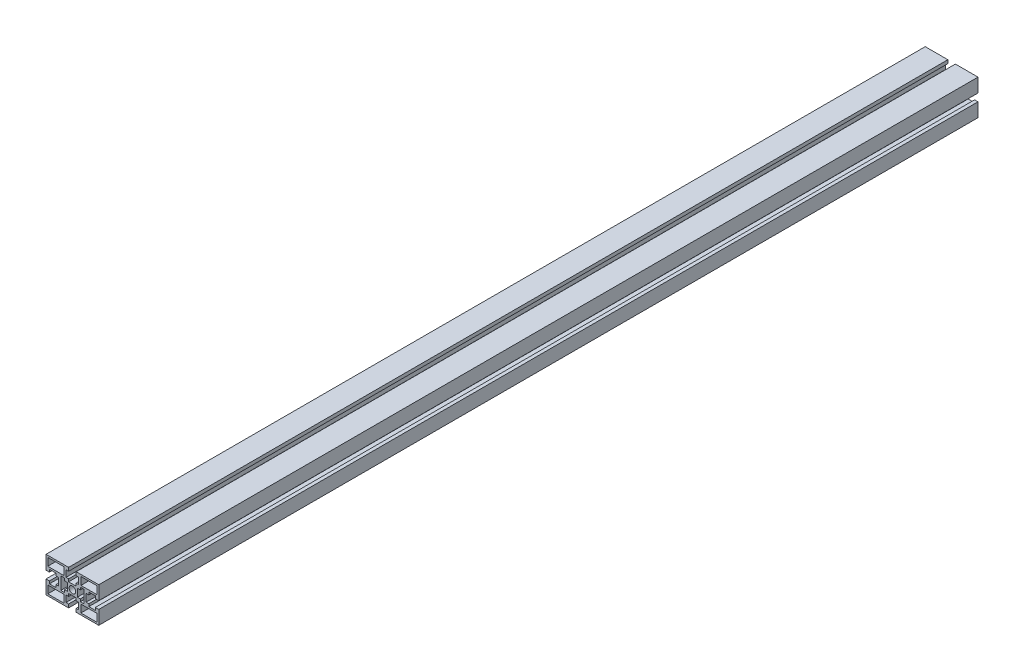
SolidWorks part; units mm, degrees
material "6063 T5"
ref_plane "Спереди" through (0, 0, 0) normal (0, 0, 1) x (1, 0, 0)
ref_plane "Сверху" through (0, 0, 0) normal (0, 1, 0) x (1, 0, 0)
ref_plane "Справа" through (0, 0, 0) normal (1, 0, 0) x (0, 0, -1)
sketch "Эскиз1" plane through (0, 0, 0) normal (0, 0, 1) x (1, 0, 0)
  line L0 (-29.9268, 29.4161) -> (30.0732, 29.4161) construction
  line L1 (0, 20) -> (0, -20) construction
  line L2 (-30, 0) -> (30, 0) construction
  line L3 (-30, 7.2) -> (-30, 20)
  line L4 (-30, 20) -> (-7.2, 20)
  line L5 (-13.2, -7.2) -> (-13.2, 7.2)
  line L6 (-28, 18) -> (-9.7, 18)
  line L7 (-28, 18) -> (-28, 9.2)
  line L8 (-28, 9.2) -> (-9.7, 9.2)
  line L9 (-9.7, 18) -> (-9.7, 9.2)
  line L10 (-13.2, 7.2) -> (-9, 7.2)
  line L11 (-9, 7.2) -> (-9, 4.4)
  line L12 (-9, 4.4) -> (-5.7, 4.4)
  line L13 (-5.7, 4.4) -> (-5.7, -4.4)
  line L14 (-9, -4.4) -> (-5.7, -4.4)
  line L15 (-9, -7.2) -> (-9, -4.4)
  line L16 (-13.2, -7.2) -> (-9, -7.2)
  line L17 (-28, -9.2) -> (-9.7, -9.2)
  line L18 (-9.7, -18) -> (-9.7, -9.2)
  line L19 (-28, -18) -> (-9.7, -18)
  line L20 (-28, -18) -> (-28, -9.2)
  line L21 (-30, -7.2) -> (-30, -20)
  line L22 (-30, -20) -> (-7.2, -20)
  line L23 (28, -18) -> (28, -9.2)
  line L24 (28, -18) -> (9.7, -18)
  line L25 (9.7, -18) -> (9.7, -9.2)
  line L26 (28, -9.2) -> (9.7, -9.2)
  line L27 (9, 4.4) -> (5.7, 4.4)
  line L28 (9, 7.2) -> (9, 4.4)
  line L29 (13.2, 7.2) -> (9, 7.2)
  line L30 (13.2, -7.2) -> (13.2, 7.2)
  line L31 (13.2, -7.2) -> (9, -7.2)
  line L32 (9, -7.2) -> (9, -4.4)
  line L33 (9, -4.4) -> (5.7, -4.4)
  line L34 (5.7, 4.4) -> (5.7, -4.4)
  line L35 (28, 9.2) -> (9.7, 9.2)
  line L36 (9.7, 18) -> (9.7, 9.2)
  line L37 (28, 18) -> (9.7, 18)
  line L38 (28, 18) -> (28, 9.2)
  line L39 (7.2, 20) -> (30, 20)
  line L40 (30, 20) -> (30, 7.2)
  line L41 (30, -7.2) -> (30, -20)
  line L42 (30, -20) -> (7.2, -20)
  circle A0 centre (0, 0) radius 3.75
  point P8 (0, 20)
  point P10 (-30, 0)
  point P25 (-5.7, 0)
  point P28 (-13.2, 0)
  line B0 (-7.2, 20) -> (-4.3, 20)
  line B1 (-4.3, 20) -> (-4.3, 16.1)
  line B2 (-4.3, 16.1) -> (-7.2, 16.1)
  line B3 (-7.2, 16.1) -> (-7.2, 8.7)
  line B4 (-7.2, 8.7) -> (-4.3, 8.7)
  line B5 (-4.3, 8.7) -> (-4.3, 5.7)
  line B6 (-4.3, 5.7) -> (4.3, 5.7)
  line B7 (4.3, 5.7) -> (4.3, 8.7)
  line B8 (4.3, 8.7) -> (7.2, 8.7)
  line B9 (7.2, 8.7) -> (7.2, 16.1)
  line B10 (7.2, 16.1) -> (4.3, 16.1)
  line B11 (4.3, 16.1) -> (4.3, 20)
  line B12 (4.3, 20) -> (7.2, 20)
  line B13 (7.2, 20) -> (-7.2, 20) construction
  line B14 (-30, -7.2) -> (-30, -4.3)
  line B15 (-30, -4.3) -> (-26.1, -4.3)
  line B16 (-26.1, -4.3) -> (-26.1, -7.2)
  line B17 (-26.1, -7.2) -> (-18.7, -7.2)
  line B18 (-18.7, -7.2) -> (-18.7, -4.3)
  line B19 (-18.7, -4.3) -> (-15.7, -4.3)
  line B20 (-15.7, -4.3) -> (-15.7, 4.3)
  line B21 (-15.7, 4.3) -> (-18.7, 4.3)
  line B22 (-18.7, 4.3) -> (-18.7, 7.2)
  line B23 (-18.7, 7.2) -> (-26.1, 7.2)
  line B24 (-26.1, 7.2) -> (-26.1, 4.3)
  line B25 (-26.1, 4.3) -> (-30, 4.3)
  line B26 (-30, 4.3) -> (-30, 7.2)
  line B27 (-30, 7.2) -> (-30, -7.2) construction
  line B28 (-7.2, -20) -> (-4.3, -20)
  line B29 (-4.3, -20) -> (-4.3, -16.1)
  line B30 (-4.3, -16.1) -> (-7.2, -16.1)
  line B31 (-7.2, -16.1) -> (-7.2, -8.7)
  line B32 (-7.2, -8.7) -> (-4.3, -8.7)
  line B33 (-4.3, -8.7) -> (-4.3, -5.7)
  line B34 (-4.3, -5.7) -> (4.3, -5.7)
  line B35 (4.3, -5.7) -> (4.3, -8.7)
  line B36 (4.3, -8.7) -> (7.2, -8.7)
  line B37 (7.2, -8.7) -> (7.2, -16.1)
  line B38 (7.2, -16.1) -> (4.3, -16.1)
  line B39 (4.3, -16.1) -> (4.3, -20)
  line B40 (4.3, -20) -> (7.2, -20)
  line B41 (7.2, -20) -> (-7.2, -20) construction
  line B42 (30, -7.2) -> (30, -4.3)
  line B43 (30, -4.3) -> (26.1, -4.3)
  line B44 (26.1, -4.3) -> (26.1, -7.2)
  line B45 (26.1, -7.2) -> (18.7, -7.2)
  line B46 (18.7, -7.2) -> (18.7, -4.3)
  line B47 (18.7, -4.3) -> (15.7, -4.3)
  line B48 (15.7, -4.3) -> (15.7, 4.3)
  line B49 (15.7, 4.3) -> (18.7, 4.3)
  line B50 (18.7, 4.3) -> (18.7, 7.2)
  line B51 (18.7, 7.2) -> (26.1, 7.2)
  line B52 (26.1, 7.2) -> (26.1, 4.3)
  line B53 (26.1, 4.3) -> (30, 4.3)
  line B54 (30, 4.3) -> (30, 7.2)
  line B55 (30, 7.2) -> (30, -7.2) construction
  dimension "D8" = 7.5
  dimension "D2" = 60
  dimension "D3" = 40
  dimension "D4" = 2
  dimension "D5" = 2.5
  dimension "D6" = 18.3
  dimension "D7" = 8.8
  dimension "D9" = 2.5
  dimension "D10" = 7.2
  dimension "D11" = 4.2
  dimension "D12" = 3.3
  dimension "D13" = 4.4
sketch_block_instance "8G(14,2U)-1"
sketch_block "8G(14,2U)" parameters "D6"=0.5, "D1"=14.4, "D2"=8.6, "D3"=2.3, "D4"=10, "D5"=4
sketch_block_instance "8G(14,2U)-3"
sketch_block_instance "8G(14,2U)-4"
sketch_block_instance "8G(14,2U)-8"
extrude "Бобышка-Вытянуть1" add sketch "Эскиз1" along normal blind 1000 contours B53 B54 L40 L39 B12 B11 B10 B9 B8 B7 B6 B5 B4 B3 B2 B1 B0 L4 L3 B26 B25 B24 B23 B22 B21 B20 B19 B18 B17 B16 B15 B14 L21 L22 B28 B29 B30 B31 B32 B33 B34 B35 B36 B37 B38 B39 B40 L42 L41 B42 B43
